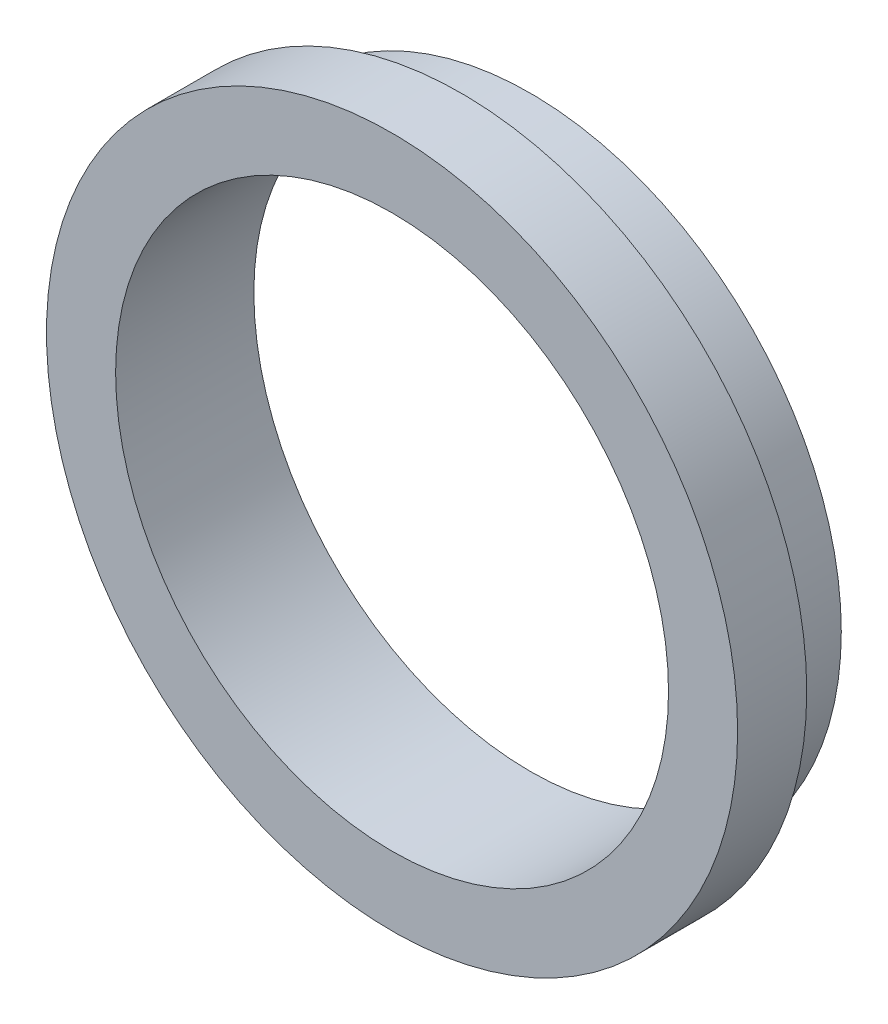
SolidWorks part; units mm, degrees
ref_plane "前视基准面" through (0, 0, 0) normal (0, 0, 1) x (1, 0, 0)
ref_plane "上视基准面" through (0, 0, 0) normal (0, 1, 0) x (1, 0, 0)
ref_plane "右视基准面" through (0, 0, 0) normal (1, 0, 0) x (0, 0, -1)
sketch "草图1" plane through (0, 0, 0) normal (0, 0, 1) x (1, 0, 0)
  circle A0 centre (0, 0) radius 4.5
  dimension "D1" = 9
extrude "凸台-拉伸1" add sketch "草图1" along normal blind 1
sketch "草图2" plane through (0, 0, 1) normal (0, 0, 1) x (1, 0, 0)
  circle A0 centre (0, 0) radius 5
  dimension "D1" = 10
extrude "凸台-拉伸2" add sketch "草图2" along normal blind 1
sketch "草图3" plane through (0, 0, 0) normal (0, 0, -1) x (-1, 0, 0)
  circle A0 centre (0, 0) radius 4
  dimension "D1" = 8
extrude "切除-拉伸1" cut sketch "草图3" against normal blind 2
